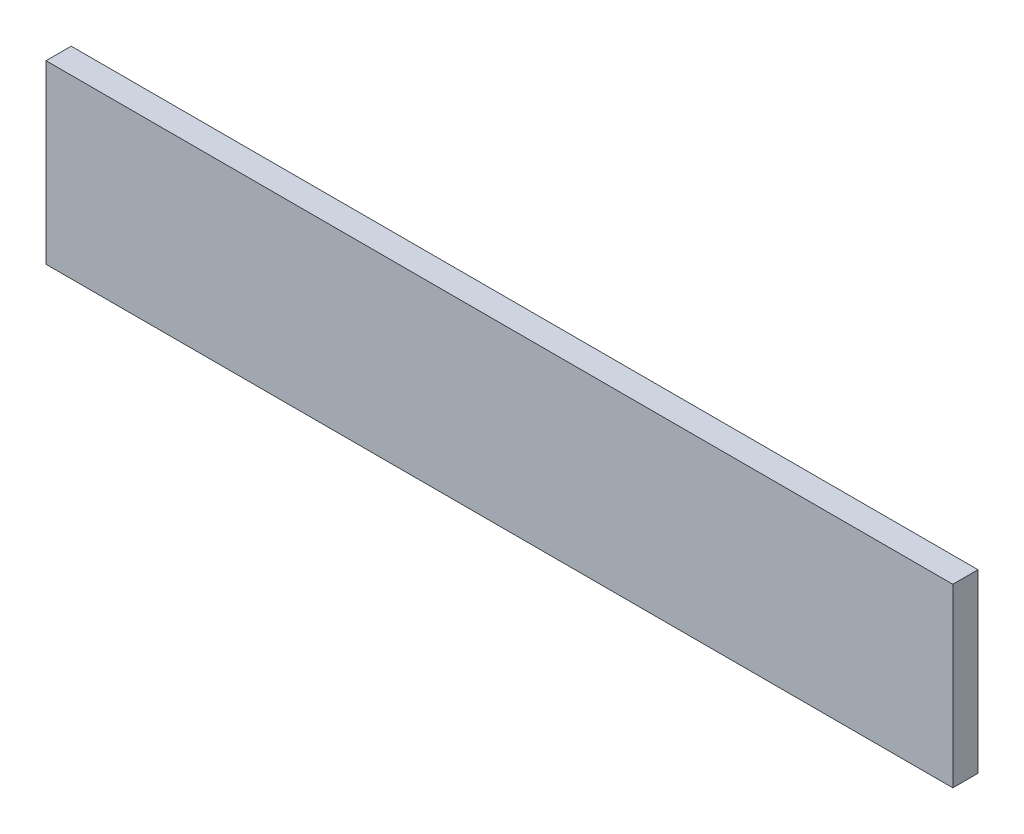
SolidWorks part; units mm, degrees
material "Acrílico (Impacto medio-alto)"
ref_plane "Alzado" through (0, 0, 0) normal (0, 0, 1) x (1, 0, 0)
ref_plane "Planta" through (0, 0, 0) normal (0, 1, 0) x (1, 0, 0)
ref_plane "Vista lateral" through (0, 0, 0) normal (1, 0, 0) x (0, 0, -1)
sketch "Croquis1" plane through (0, 0, 0) normal (0, 0, 1) x (1, 0, 0)
  line L1 (0, 0) -> (180, 0)
  line L2 (0, 0) -> (0, 35)
  line L3 (0, 35) -> (180, 35)
  line L4 (180, 0) -> (180, 35)
  dimension "D1" = 35
  dimension "D2" = 180
extrude "Saliente-Extruir1" add sketch "Croquis1" along normal blind 5
